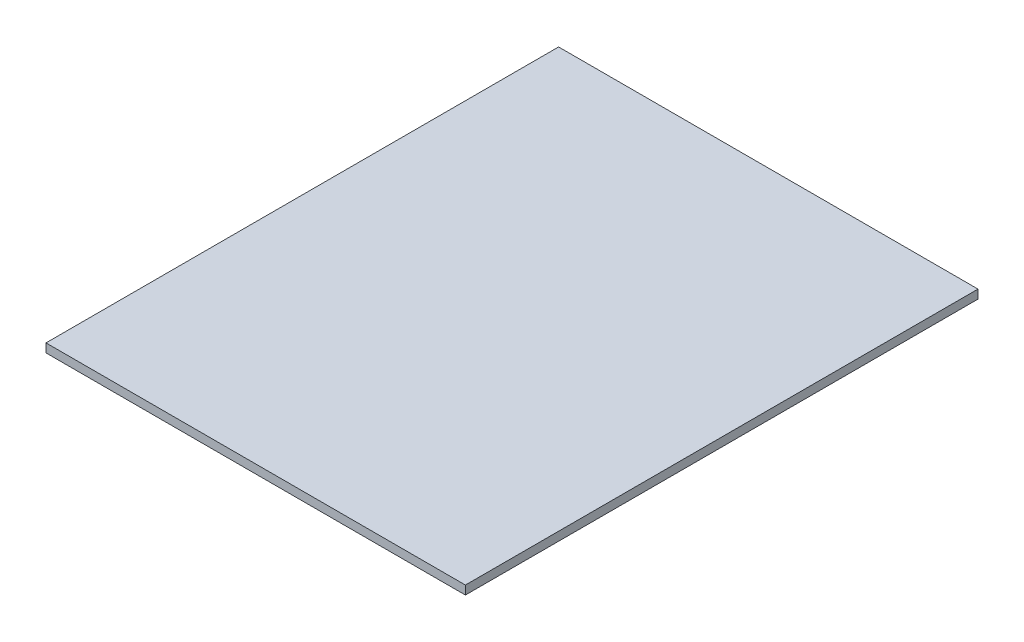
SolidWorks part; units mm, degrees
ref_plane "Front Plane" through (0, 0, 0) normal (0, 0, 1) x (1, 0, 0)
ref_plane "Top Plane" through (0, 0, 0) normal (0, 1, 0) x (1, 0, 0)
ref_plane "Right Plane" through (0, 0, 0) normal (1, 0, 0) x (0, 0, -1)
sketch "Sketch1" plane through (0, 0, 0) normal (0, 1, 0) x (1, 0, 0)
  line L1 (-67.5, -82.5) -> (67.5, -82.5)
  line L2 (-67.5, -82.5) -> (-67.5, 82.5)
  line L3 (-67.5, 82.5) -> (67.5, 82.5)
  line L4 (67.5, -82.5) -> (67.5, 82.5)
  line L5 (-67.5, -82.5) -> (67.5, 82.5) construction
  line L6 (-67.5, 82.5) -> (67.5, -82.5) construction
  point P0 (0, 0)
  dimension "D1" = 165
  dimension "D2" = 135
extrude "Boss-Extrude1" add sketch "Sketch1" along normal blind 2.8 contours L3 L4 L1 L2
